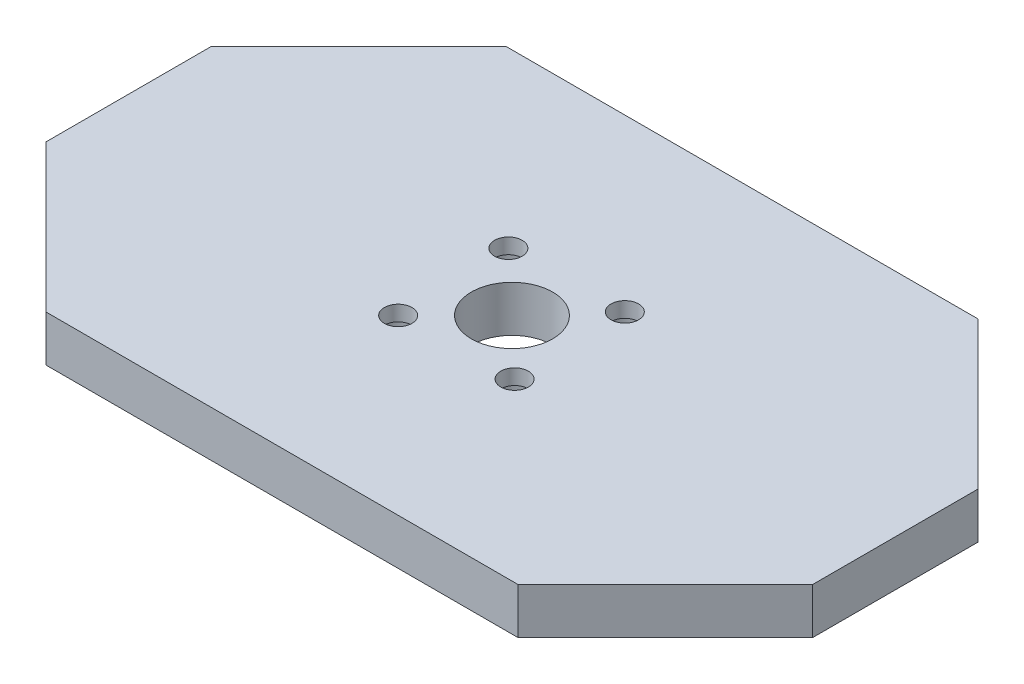
SolidWorks part; units mm, degrees
ref_plane "Alzado" through (0, 0, 0) normal (0, 0, 1) x (1, 0, 0)
ref_plane "Planta" through (0, 0, 0) normal (0, 1, 0) x (1, 0, 0)
ref_plane "Vista lateral" through (0, 0, 0) normal (1, 0, 0) x (0, 0, -1)
sketch "Croquis1" plane through (0, 0, 0) normal (0, 1, 0) x (1, 0, 0)
  line L0 (-50, 10.7839) -> (-30.7839, 30)
  line L1 (-30.7839, 30) -> (30.7839, 30)
  line L2 (-50, 10.7839) -> (-50, -10.7839)
  line L3 (-30.7839, -30) -> (30.7839, -30)
  line L4 (50, 10.7839) -> (50, -10.7839)
  line L5 (-50, 30) -> (50, -30) construction
  line L6 (-50, -30) -> (50, 30) construction
  line L7 (30.7839, 30) -> (50, 10.7839)
  line L8 (50, -10.7839) -> (30.7839, -30)
  line L9 (-50, -10.7839) -> (-30.7839, -30)
  line L10 (-50, 30) -> (-30.7839, 30) construction
  line L11 (-50, 30) -> (-50, 10.7839) construction
  line L12 (30.7839, 30) -> (50, 30) construction
  line L13 (50, 30) -> (50, 10.7839) construction
  line L14 (50, -10.7839) -> (50, -30) construction
  line L15 (50, -30) -> (30.7839, -30) construction
  line L16 (-30.7839, -30) -> (-50, -30) construction
  line L17 (-50, -30) -> (-50, -10.7839) construction
  line L18 (50, 0) -> (-50, 0) construction
  line L19 (0, -30) -> (0, 30) construction
  line L20 (30.7839, -30) -> (30.7839, 30) construction
  line L21 (-30.7839, -30) -> (-30.7839, 30) construction
  point P0 (0, 0)
  dimension "D1" = 60
  dimension "D2" = 100
  dimension "D3" = 45
extrude "Saliente-Extruir1" add sketch "Croquis1" along normal blind 6
sketch "Croquis2" plane through (0, 6, 0) normal (0, 1, 0) x (1, 0, 0)
  line L0 (50, 0) -> (-50, 0) construction
  line L1 (50, -10.7839) -> (50, 10.7839) construction
  line L2 (-50, 10.7839) -> (-50, -10.7839) construction
  line L3 (0, 30) -> (0, -30) construction
  line L4 (30.7839, 30) -> (-30.7839, 30) construction
  line L5 (-30.7839, -30) -> (30.7839, -30) construction
  line L6 (0, 0) -> (-7.4246, -7.4246) construction
  circle A0 centre (0, 0) radius 5.3
  circle A1 centre (0, 0) radius 10.5 construction
  circle A2 centre (-7.4246, -7.4246) radius 1.8
  circle A3 centre (-7.8277, 7.3574) radius 1.8
  circle A4 centre (6.9543, 7.7605) radius 1.8
  circle A5 centre (7.3574, -7.0215) radius 1.8
  point P26 (-0.2352, 0.168)
  dimension "D1" = 10.6
  dimension "D2" = 21
  dimension "D3" = 3.6
  dimension "D4" = 45
  dimension "D5" = 4
extrude "Cortar-Extruir1" cut sketch "Croquis2" against normal up to next
sketch "Croquis3" plane through (0, 0, 0) normal (0, -1, 0) x (1, 0, 0)
  circle A0 centre (7.3574, 7.0215) radius 4
  circle A1 centre (6.9543, -7.7605) radius 2.9109
  circle A2 centre (-7.4246, 7.4246) radius 2.9788
  circle A3 centre (-7.8277, -7.3574) radius 4
  dimension "D1" = 8
extrude "Cortar-Extruir2" cut sketch "Croquis3" against normal offset from surface (4 mm away) 2 up to face at (7.3574, 6, 8.8215)
